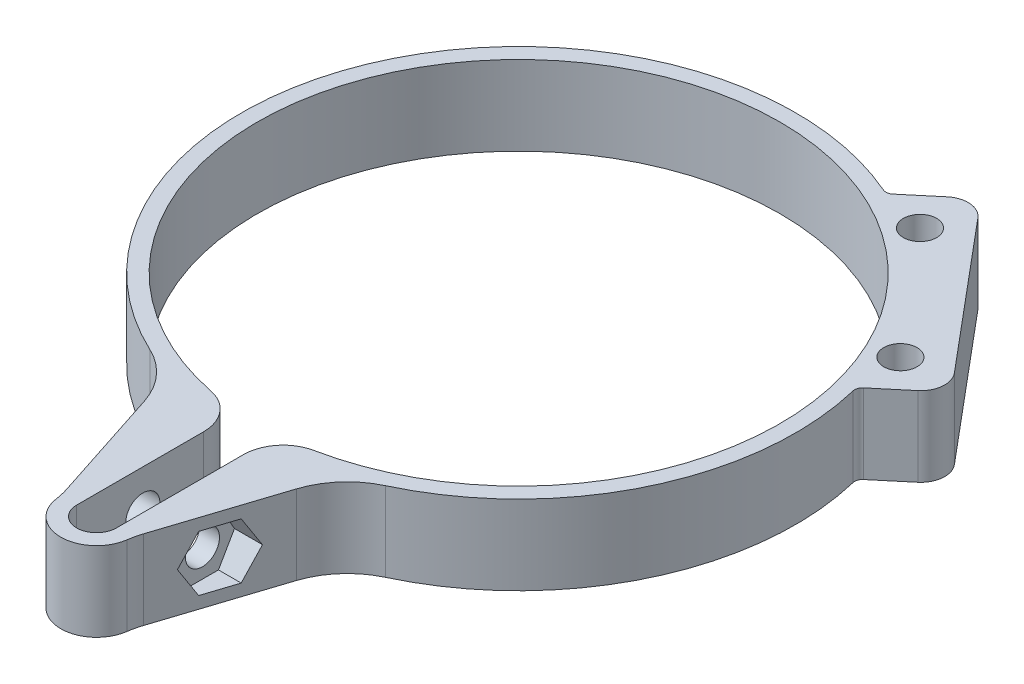
SolidWorks part; units mm, degrees
ref_plane "Front Plane" through (0, 0, 0) normal (0, 0, 1) x (1, 0, 0)
ref_plane "Top Plane" through (0, 0, 0) normal (0, 1, 0) x (1, 0, 0)
ref_plane "Right Plane" through (0, 0, 0) normal (1, 0, 0) x (0, 0, -1)
sketch "Sketch1" plane through (0, 0, 0) normal (0, 1, 0) x (1, 0, 0)
  line L0 (0, 0) -> (44.0628, 36.973) construction
  line L1 (22.9283, 34.904) -> (38.3552, 16.519)
  line L2 (18.7018, 35.2738) -> (14.9811, 32.1518)
  line L4 (37.9855, 12.2925) -> (34.2647, 9.1704)
  line L5 (-2.5, -37.1556) -> (-2.5, -53.1556)
  line L11 (-4.8483, -52.0837) -> (-9.5671, -37.5608)
  line L12 (2.5, -37.1556) -> (2.5, -53.1556)
  line L13 (0, -33.8126) -> (0, -59.9533) construction
  line L15 (4.8483, -52.0837) -> (9.5671, -37.5608)
  line L16 (20.3837, 30.158) -> (33.2394, 14.8371) construction
  line L17 (0, 0) -> (32.905, 0) construction
  arc A0 (6.5107, -32.2545) -> (-6.5107, -32.2545) centre (0, 0) ccw
  arc A1 (13.939, 32.001) -> (-14.8292, -31.5983) centre (0, 0) ccw
  arc A2 (14.8292, -31.5983) -> (33.9353, 8.1703) centre (0, 0) ccw
  arc A3 (-4.4562, -53.782) -> (0, -57.6556) centre (0, -53.1556) ccw
  arc A4 (-2.5, -53.1556) -> (2.5, -53.1556) centre (0, -53.1556) ccw
  arc A5 (4.4562, -53.782) -> (0, -57.6556) centre (0, -53.1556) cw
  arc A6 (-9.5671, -37.5608) -> (-14.8292, -31.5983) centre (-19.0776, -40.651) ccw
  arc A7 (-4.4562, -53.782) -> (-4.8483, -52.0837) centre (-14.3589, -55.1739) ccw
  arc A8 (4.4562, -53.782) -> (4.8483, -52.0837) centre (14.3589, -55.1739) cw
  arc A9 (9.5671, -37.5608) -> (14.8292, -31.5983) centre (19.0776, -40.651) cw
  arc A10 (6.5107, -32.2545) -> (2.5, -37.1556) centre (7.5, -37.1556) ccw
  arc A11 (-2.5, -37.1556) -> (-6.5107, -32.2545) centre (-7.5, -37.1556) ccw
  circle A12 centre (20.3837, 30.158) radius 2.1
  circle A13 centre (33.2394, 14.8371) radius 2.1
  arc A14 (38.3552, 16.519) -> (37.9855, 12.2925) centre (36.0571, 14.5906) cw
  arc A15 (22.9283, 34.904) -> (18.7018, 35.2738) centre (20.6302, 32.9757) ccw
  arc A16 (33.9353, 8.1703) -> (34.2647, 9.1704) centre (34.9075, 8.4044) cw
  arc A17 (13.939, 32.001) -> (14.9811, 32.1518) centre (14.3383, 32.9178) ccw
  point P20 (-11.0088, -33.1235)
  point P30 (-4.5, -53.1556)
  point P33 (4.5, -53.1556)
  point P36 (11.0088, -33.1235)
  dimension "D1" = 65.81
  dimension "D4" = 10
  dimension "D5" = 5
  dimension "D6" = 4.2
  dimension "D10" = 3
  dimension "D11" = 1
  dimension "D16" = 2.5
  dimension "D2" = 2
  dimension "D3" = 5
  dimension "D7" = 5
  dimension "D9" = 40
  dimension "D13" = 20
  dimension "D8" = 5
  dimension "D12" = 18
  dimension "D14" = 2
  dimension "D15" = 16
  dimension "D17" = 30
  dimension "D18" = 40
extrude "Boss-Extrude1" add sketch "Sketch1" along normal blind 10
sketch "Sketch3" plane through (0, 0, 0) normal (1, 0, 0) x (0, 0, -1)
  line L0 (-44.8223, 10) -> (-44.8223, 0) construction
  line L1 (-52.0837, 10) -> (-37.5608, 10) construction
  line L2 (-52.0837, 0) -> (-37.5608, 0) construction
  circle A0 centre (-44.8223, 5) radius 2.15
  dimension "D1" = 4.3
extrude "Cut-Extrude1" cut sketch "Sketch3" against normal blind 10 and the other way blind 10
sketch "Sketch4" plane through (0, 0, 0) normal (1, 0, 0) x (0, 0, -1)
  circle A0 centre (-44.8223, 5) radius 3.75
  dimension "D1" = 7.5
extrude "Cut-Extrude2" cut sketch "Sketch4" against normal blind 10 from offset 6 offset against normal yes
sketch "Sketch5" plane through (2.5, 0, 0) normal (-1, 0, 0) x (0, 0, 1)
  line L0 (52.0837, 0) -> (37.5608, 0) construction
  line L1 (46.843, 8.5) -> (42.8015, 8.5)
  line L2 (42.8015, 8.5) -> (40.7808, 5)
  line L3 (40.7808, 5) -> (42.8015, 1.5)
  line L4 (42.8015, 1.5) -> (46.843, 1.5)
  line L5 (46.843, 1.5) -> (48.8637, 5)
  line L6 (48.8637, 5) -> (46.843, 8.5)
  circle A0 centre (44.8223, 5) radius 3.5 construction
  dimension "D1" = 7
extrude "Cut-Extrude3" cut sketch "Sketch5" against normal blind 10 from offset 2.5
equation "\"D16@Sketch1\"=\"D3@Sketch1\"/2"
